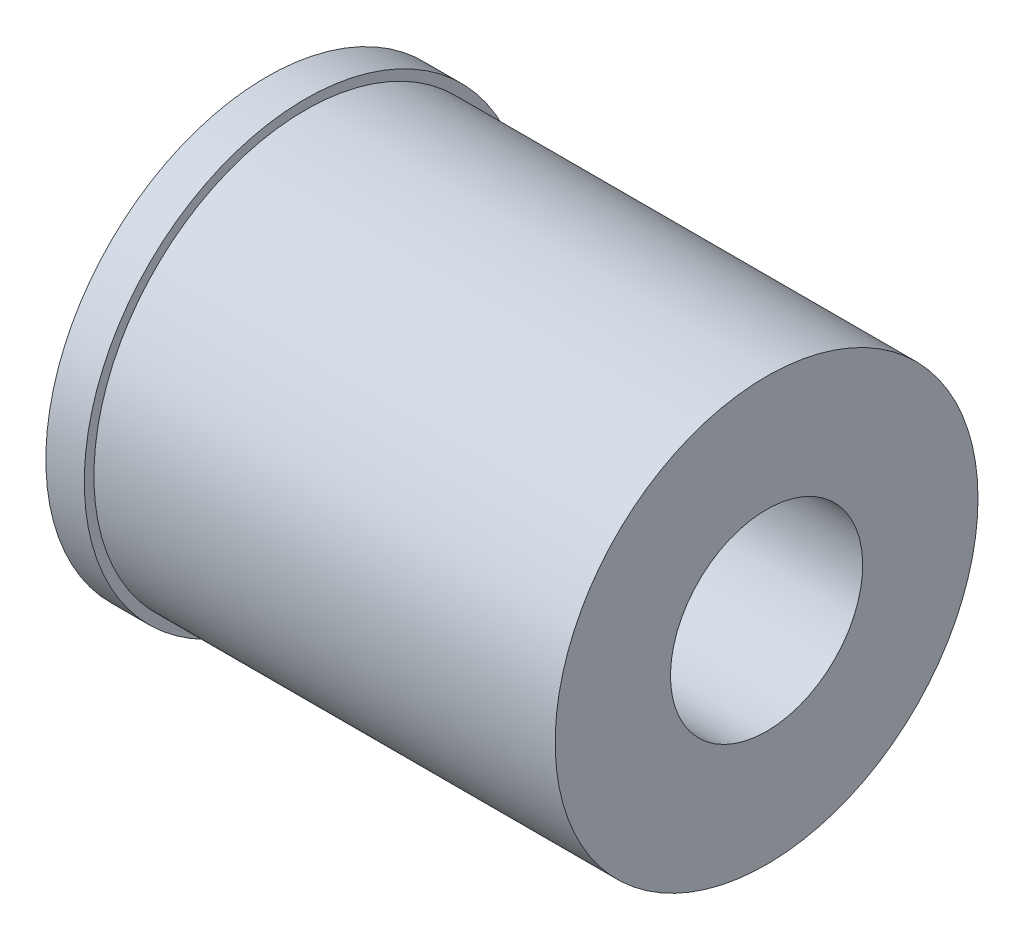
SolidWorks part; units mm, degrees
ref_plane "正面" through (0, 0, 0) normal (0, 0, 1) x (1, 0, 0)
ref_plane "平面" through (0, 0, 0) normal (0, 1, 0) x (1, 0, 0)
ref_plane "右側面" through (0, 0, 0) normal (1, 0, 0) x (0, 0, -1)
sketch "ｽｹｯﾁ1" plane through (0, 0, 0) normal (0, 0, 1) x (1, 0, 0)
  line L0 (-13, 5.75) -> (-13, 0)
  line L1 (-13, -5.75) -> (-10, -5.75) construction
  line L2 (-10, -5.75) -> (-10, -5.5) construction
  line L3 (-10, -5.5) -> (0, -5.5) construction
  line L4 (0, 0) -> (0, 5.5)
  line L5 (0, 5.5) -> (-12, 5.5)
  line L6 (-12, 5.5) -> (-12, 5.75)
  line L7 (-12, 5.75) -> (-13, 5.75)
  line L8 (0, 0) -> (-13, 0)
  line L9 (-13, 0) -> (-13, -5.75) construction
  line L10 (0, -5.5) -> (0, 0) construction
  point P11 (-13, 0)
  dimension "D1" = 11
  dimension "D2" = 11.5
  dimension "D3" = 12
  dimension "D4" = 1
  dimension "D5" = 3
  dimension "D6" = 0.25
revolve "回転1" add sketch "ｽｹｯﾁ1" angle 360 about L8
sketch "ｽｹｯﾁ2" plane through (-13, 0, 0) normal (-1, 0, 0) x (0, 0, 1)
  circle A0 centre (0, 0) radius 2.5
  dimension "D1" = 5
extrude "ｶｯﾄ - 押し出し1" cut sketch "ｽｹｯﾁ2" against normal through all contours A0
